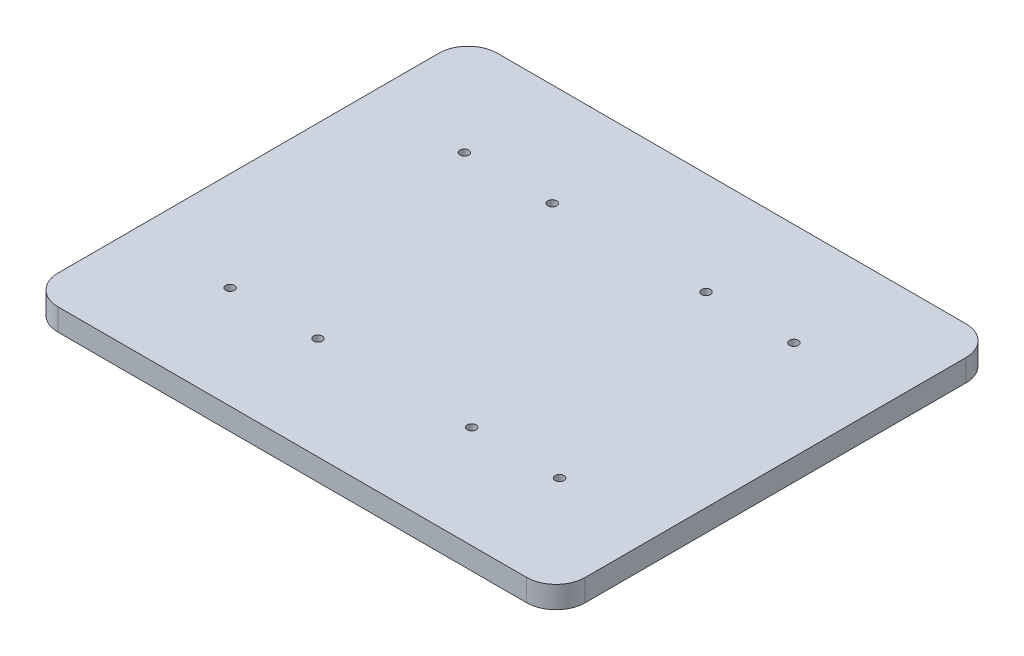
SolidWorks part; units mm, degrees
ref_plane "Front Plane" through (0, 0, 0) normal (0, 0, 1) x (1, 0, 0)
ref_plane "Top Plane" through (0, 0, 0) normal (0, 1, 0) x (1, 0, 0)
ref_plane "Right Plane" through (0, 0, 0) normal (1, 0, 0) x (0, 0, -1)
sketch "Sketch2" plane through (0, 0, 0) normal (0, 1, 0) x (1, 0, 0)
  line L1 (-180, -150) -> (180, -150)
  line L2 (-180, -150) -> (-180, 150)
  line L3 (-180, 150) -> (180, 150)
  line L4 (180, -150) -> (180, 150)
  line L5 (-180, -150) -> (180, 150) construction
  line L6 (-180, 150) -> (180, -150) construction
  point P0 (0, 0)
  dimension "D1" = 360
  dimension "D2" = 300
extrude "Boss-Extrude1" add sketch "Sketch2" along normal blind 15
fillet "Fillet1" radius 20 4 edges at (-180, 7.5, -150) (180, 7.5, -150) (-180, 7.5, 150) (180, 7.5, 150)
sketch "Sketch3" plane through (0, 15, 0) normal (0, 1, 0) x (1, 0, 0)
  line L0 (-52.5, 80) -> (-52.5, -80) construction
  line L1 (-112.5, -80) -> (112.5, -80) construction
  line L2 (-112.5, -80) -> (-112.5, 80) construction
  line L3 (-112.5, 80) -> (112.5, 80) construction
  line L4 (112.5, -80) -> (112.5, 80) construction
  line L5 (-112.5, -80) -> (112.5, 80) construction
  line L6 (-112.5, 80) -> (112.5, -80) construction
  line L7 (52.5, 80) -> (52.5, -80) construction
  point P0 (0, 0)
  dimension "D1" = 160
  dimension "D2" = 225
  dimension "D3" = 60
  dimension "D4" = 60
hole_wizard "Ø6.0mm Dowel Hole1" positions "3DSketch1" profile "Sketch4" hole size "Ø6.0" standard "KS" end condition up to next
sketch3d "3DSketch1"
  point P0 (-112.5, 15, 80)
  point P3 (-52.5, 15, 80)
  point P6 (52.5, 15, 80)
  point P9 (112.5, 15, 80)
  point P12 (112.5, 15, -80)
  point P15 (52.5, 15, -80)
  point P18 (-52.5, 15, -80)
  point P21 (-112.5, 15, -80)
sketch "Sketch4" plane through (-112.5, 15, 80) normal (1, 0, 0) x (0, 0, 1)
  line L0 (0, 0) -> (0, 15)
  line L1 (0, 15) -> (3, 15)
  line L2 (3, 15) -> (3, 0)
  line L5 (3, 0) -> (0, 0)
  line L11 (0, -6.35) -> (0, 107.95) construction
  dimension "Thru Hole Dia." = 6
  dimension "Thru Hole Depth" = 15
